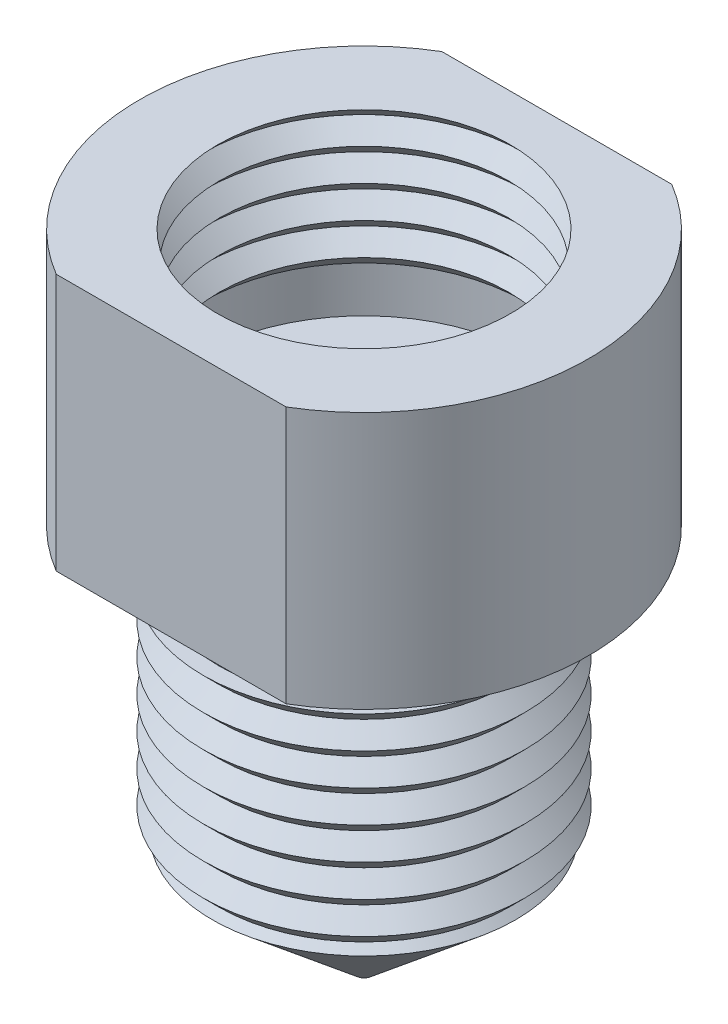
SolidWorks part; units mm, degrees
material "6061-T6 (SS)"
ref_plane "Front Plane" through (0, 0, 0) normal (0, 0, 1) x (1, 0, 0)
ref_plane "Top Plane" through (0, 0, 0) normal (0, 1, 0) x (1, 0, 0)
ref_plane "Right Plane" through (0, 0, 0) normal (1, 0, 0) x (0, 0, -1)
sketch "Sketch1" plane through (0, 0, 0) normal (0, 0, 1) x (1, 0, 0)
  line L0 (0, 0) -> (0, -41.223) construction
  line L1 (5, 0) -> (5, -5.969) construction
  line L2 (5.1435, -5.969) -> (1.5875, -5.969)
  line L3 (1.5875, -5.969) -> (1.5875, -17.906)
  line L4 (1.5875, -17.906) -> (0.25, -19.5)
  line L5 (0.25, -19.5) -> (0.25, -20)
  line L6 (5, -4.445) -> (5.1435, -4.445)
  line L7 (5.1435, -4.445) -> (5.1435, -5.969)
  line L8 (4.5, -15.025) -> (5, -15.525)
  line L9 (0.25, -20) -> (4.7223, -16.2473)
  line L10 (5, -16.129) -> (5, -9.525) construction
  line L11 (5, -9.525) -> (4.5, -9.525)
  line L12 (4.5, -9.525) -> (4.5, -8.001)
  line L13 (4.5, -8.001) -> (6.985, -8.001)
  line L14 (6.985, -8.001) -> (6.985, 0)
  line L15 (6.985, 0) -> (4.555, 0)
  line L16 (4.5, -9.525) -> (4.5, -17.0698) construction
  line L17 (5, -9.525) -> (4.5, -10.025)
  line L18 (4.5, -10.025) -> (5, -10.525)
  line L19 (5, -10.525) -> (4.5, -11.025)
  line L20 (4.5, -11.025) -> (5, -11.525)
  line L21 (5, -11.525) -> (4.5, -12.025)
  line L22 (4.5, -12.025) -> (5, -12.525)
  line L23 (5, -12.525) -> (4.5, -13.025)
  line L24 (4.5, -13.025) -> (5, -13.525)
  line L25 (5, -13.525) -> (4.5, -14.025)
  line L26 (4.5, -14.025) -> (5, -14.525)
  line L27 (5, -14.525) -> (4.5, -15.025)
  line L28 (5, -15.525) -> (4.5, -16.025)
  line L29 (4.5, -9.525) -> (4.5, 0) construction
  line L30 (4.5, -16.025) -> (4.7223, -16.2473)
  line L32 (5, -4.445) -> (4.5, -3.945)
  line L33 (4.5, -3.945) -> (5, -3.445)
  line L34 (5, -3.445) -> (4.5, -2.945)
  line L35 (4.5, -2.945) -> (5, -2.445)
  line L36 (5, -2.445) -> (4.5, -1.945)
  line L37 (4.5, -1.945) -> (5, -1.445)
  line L38 (5, -1.445) -> (4.5, -0.945)
  line L39 (4.5, -0.945) -> (5, -0.445)
  line L40 (5, -0.445) -> (4.555, 0)
  dimension "D1" = 13.97
  dimension "D2" = 3.175
  dimension "D3" = 5
  dimension "D4" = 9
  dimension "D5" = 50
  dimension "D6" = 8.001
  dimension "D7" = 5.969
  dimension "D8" = 1.524
  dimension "D9" = 20
  dimension "D10" = 0.5
  dimension "D11" = 0.5
  dimension "D12" = 1.524
  dimension "D13" = 1
  dimension "D14" = 40
  dimension "D15" = 0.5
  dimension "D16" = 1
  dimension "D17" = 0.5
  dimension "D18" = 10.287
revolve "Revolve1" add sketch "Sketch1" angle 360 about L0
sketch "Sketch2" plane through (0, 0, 0) normal (0, 1, 0) x (1, 0, 0)
  line L0 (-10.2759, 0) -> (0, 0) construction
  line L1 (-10.2759, 6) -> (11.5097, 6)
  line L2 (-10.2759, 6) -> (-10.2759, -6)
  line L3 (-10.2759, -6) -> (11.5097, -6)
  line L4 (11.5097, 6) -> (11.5097, -6)
  dimension "D1" = 12
extrude "Cut-Extrude1" cut sketch "Sketch2" against normal through all flip side to cut
